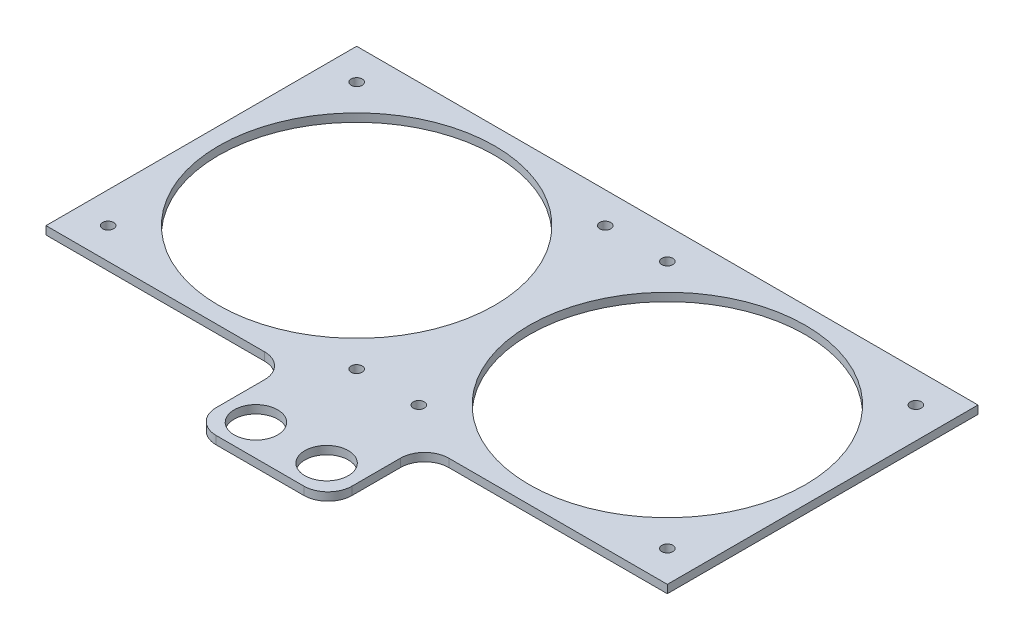
SolidWorks part; units mm, degrees
other "Markup1"
sketch "Sketch2" plane through (228.6, 3, 0) normal (0.0288, 0.7389, 0.6732) x (0.9897, 0.0732, -0.1227)
ref_plane "Front Plane" through (0, 0, 0) normal (0, 0, 1) x (1, 0, 0)
ref_plane "Top Plane" through (0, 0, 0) normal (0, 1, 0) x (1, 0, 0)
ref_plane "Right Plane" through (0, 0, 0) normal (1, 0, 0) x (0, 0, -1)
sketch "Sketch1" plane through (0, 0, 0) normal (0, 1, 0) x (1, 0, 0)
  line L0 (57.15, 114.3) -> (57.15, 0) construction
  line L1 (0, 0) -> (114.3, 0)
  line L2 (0, 0) -> (0, 114.3)
  line L3 (0, 114.3) -> (114.3, 114.3)
  line L4 (114.3, 0) -> (114.3, 114.3)
  line L6 (11.43, 102.87) -> (102.87, 102.87) construction
  line L7 (11.43, 102.87) -> (11.43, 11.43) construction
  line L8 (11.43, 11.43) -> (102.87, 11.43) construction
  line L9 (102.87, 102.87) -> (102.87, 11.43) construction
  line L10 (11.43, 102.87) -> (102.87, 11.43) construction
  line L11 (11.43, 11.43) -> (102.87, 102.87) construction
  circle A0 centre (57.15, 57.15) radius 50.8
  circle A1 centre (11.43, 102.87) radius 2.032
  circle A2 centre (102.87, 102.87) radius 2.032
  circle A3 centre (102.87, 11.43) radius 2.032
  circle A4 centre (11.43, 11.43) radius 2.032
  dimension "D2" = 101.6
  dimension "D3" = 4.064
  dimension "D1" = 114.3
  dimension "D4" = 91.44
extrude "Boss-Extrude1" add sketch "Sketch1" along normal blind 3
mirror "Mirror1" about plane through (114.3, 3, 0) normal (-1, 0, 0) of "Boss-Extrude1"
sketch "Sketch3" plane through (0, 0, 0) normal (0, 0, 1) x (1, 0, 0)
  line L0 (114.3, 3) -> (114.3, 0) construction
  line L1 (0, 3) -> (228.6, 3) construction
  line L2 (0, 0) -> (228.6, 0) construction
  line L4 (89.3, 3) -> (139.3, 3)
  line L5 (89.3, 3) -> (89.3, 0)
  line L6 (89.3, 0) -> (139.3, 0)
  line L7 (139.3, 3) -> (139.3, 0)
  line L8 (89.3, 3) -> (139.3, 0) construction
  line L9 (89.3, 0) -> (139.3, 3) construction
  point P6 (114.3, 1.5)
  dimension "D1" = 50
extrude "Boss-Extrude2" add sketch "Sketch3" along normal blind 35.56
sketch "Sketch4" plane through (0, 3, 0) normal (0, 1, 0) x (1, 0, 0)
  line L0 (114.3, 114.3) -> (114.3, -35.56) construction
  line L1 (228.6, 114.3) -> (0, 114.3) construction
  line L2 (139.3, -35.56) -> (89.3, -35.56) construction
  line L3 (101.3, -24.06) -> (127.3, -24.06) construction
  circle A0 centre (101.3, -24.06) radius 8
  circle A1 centre (127.3, -24.06) radius 8
  point P8 (114.3, -24.06)
  dimension "D1" = 16
  dimension "D2" = 10
  dimension "D3" = 11.5
extrude "Cut-Extrude1" cut sketch "Sketch4" against normal through all
fillet "Fillet2" radius 8.89 4 edges at (139.3, 1.5, 0) (89.3, 1.5, 0) (139.3, 1.5, 35.56) (89.3, 1.5, 35.56)
